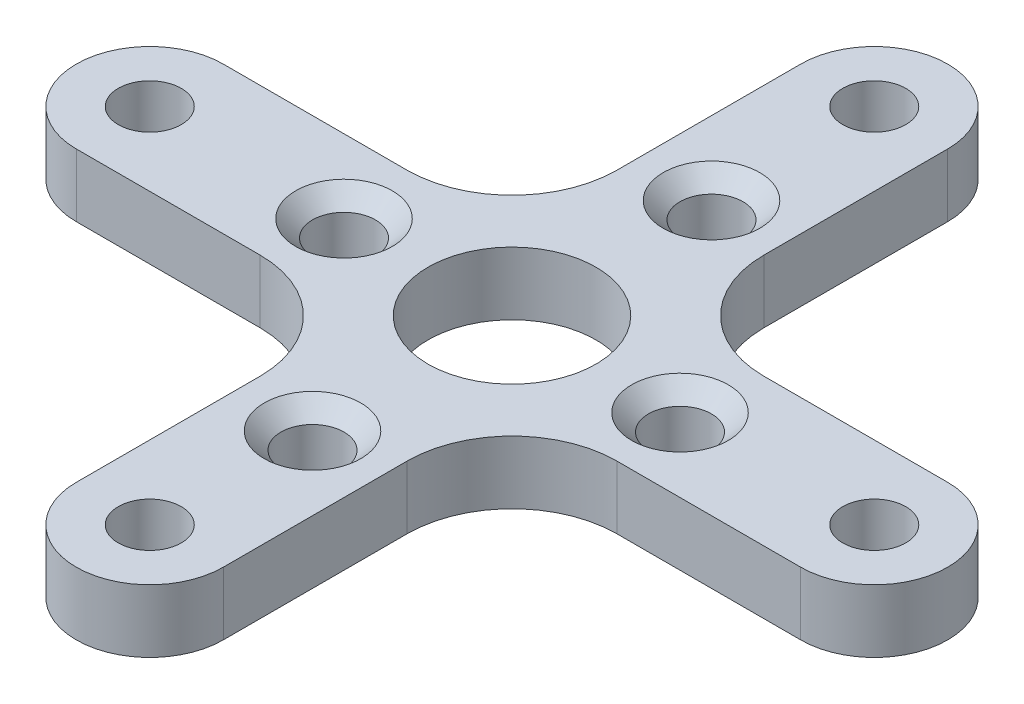
SolidWorks part; units mm, degrees
ref_plane "Front Plane" through (0, 0, 0) normal (0, 0, 1) x (1, 0, 0)
ref_plane "Top Plane" through (0, 0, 0) normal (0, 1, 0) x (1, 0, 0)
ref_plane "Right Plane" through (0, 0, 0) normal (1, 0, 0) x (0, 0, -1)
sketch "Sketch1" plane through (0, 0, 0) normal (0, 1, 0) x (1, 0, 0)
  line L0 (-3.5, 17.25) -> (-3.5, 8.5)
  line L1 (3.5, 17.25) -> (3.5, 8.5)
  line L2 (17.25, 3.5) -> (8.5, 3.5)
  line L3 (17.25, -3.5) -> (8.5, -3.5)
  line L4 (3.5, -17.25) -> (3.5, -8.5)
  line L5 (-3.5, -17.25) -> (-3.5, -8.5)
  line L6 (-17.25, -3.5) -> (-8.5, -3.5)
  line L7 (-17.25, 3.5) -> (-8.5, 3.5)
  circle A0 centre (0, 0) radius 4
  arc A1 (3.5, 17.25) -> (-3.5, 17.25) centre (0, 17.25) ccw
  circle A2 centre (0, 17.25) radius 1.5
  arc A3 (17.25, -3.5) -> (17.25, 3.5) centre (17.25, 0) ccw
  circle A4 centre (17.25, 0) radius 1.5
  arc A5 (-3.5, -17.25) -> (3.5, -17.25) centre (0, -17.25) ccw
  circle A6 centre (0, -17.25) radius 1.5
  arc A7 (-17.25, 3.5) -> (-17.25, -3.5) centre (-17.25, 0) ccw
  circle A8 centre (-17.25, 0) radius 1.5
  arc A9 (-8.5, -3.5) -> (-3.5, -8.5) centre (-8.5, -8.5) cw
  arc A10 (-8.5, 3.5) -> (-3.5, 8.5) centre (-8.5, 8.5) ccw
  arc A11 (8.5, 3.5) -> (3.5, 8.5) centre (8.5, 8.5) cw
  arc A12 (3.5, -8.5) -> (8.5, -3.5) centre (8.5, -8.5) cw
  circle A13 centre (-8, 0) radius 1.5
  circle A14 centre (8, 0) radius 1.5
  circle A15 centre (0, 9.5) radius 1.5
  circle A16 centre (0, -9.5) radius 1.5
  point P30 (0, 0)
  point P42 (0.8625, 1.1595)
  dimension "D1" = 8
  dimension "D2" = 7
  dimension "D4" = 3
  dimension "D6" = 5
  dimension "D7" = 5
  dimension "D8" = 3
  dimension "D9" = 3
  dimension "D10" = 3
  dimension "D11" = 3
  dimension "D3" = 17.25
  dimension "D12" = 8
  dimension "D13" = 8
  dimension "D14" = 9.5
  dimension "D15" = 9.5
  dimension "D5" = 4
extrude "Boss-Extrude1" add sketch "Sketch1" along normal blind 3
chamfer "Chamfer1" distance 0.8 angle 45 4 edges at (0, 3, 11) (-8, 3, 1.5) (8, 3, 1.5) (0, 3, -8)
